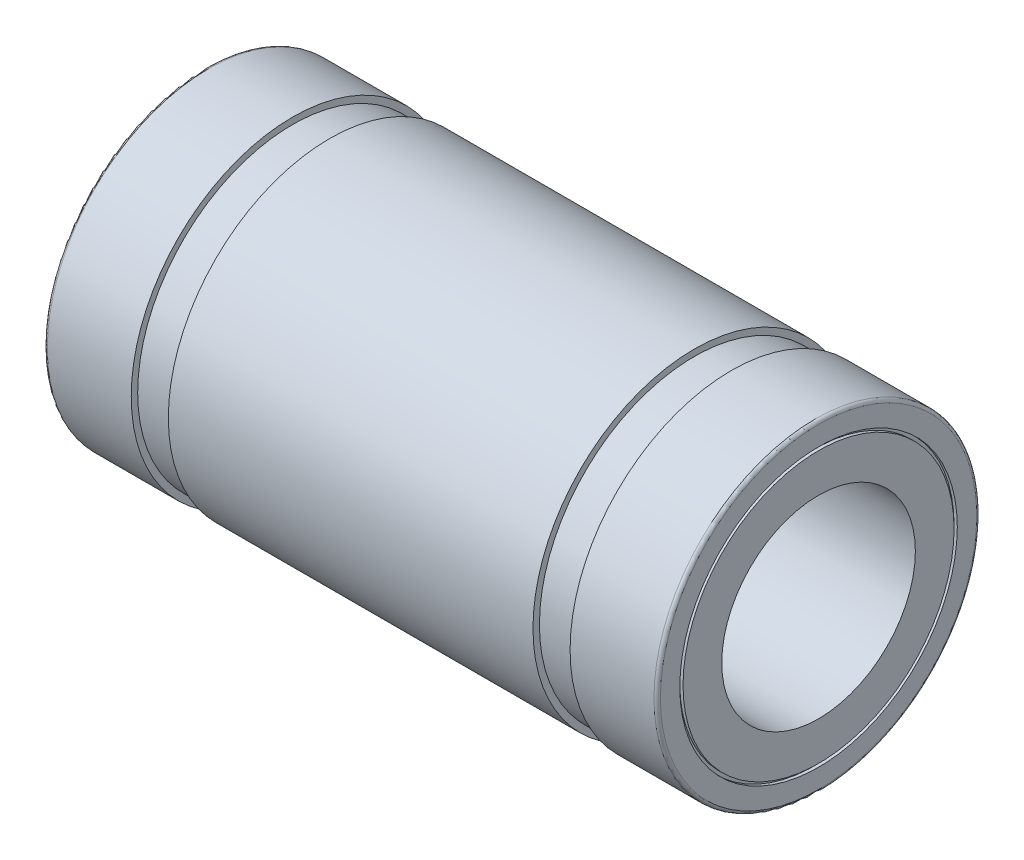
SolidWorks part; units mm, degrees
ref_plane "Front Plane" through (0, 0, 0) normal (0, 0, 1) x (1, 0, 0)
ref_plane "Top Plane" through (0, 0, 0) normal (0, 1, 0) x (1, 0, 0)
ref_plane "Right Plane" through (0, 0, 0) normal (1, 0, 0) x (0, 0, -1)
ref_plane "Plane1" through (0, 0, 0) normal (0, 0, -1) x (-1, 0, 0)
sketch "Sketch1" plane through (0, 0, 0) normal (0, 0, -1) x (-1, 0, 0)
  line L0 (-9.4, 4.2) -> (-9.5, 4.2)
  line L1 (-9.5, 4.2) -> (-9.5, 3)
  line L2 (-9.5, 3) -> (9.5, 3)
  line L3 (9.5, 3) -> (9.5, 4.2)
  line L4 (9.5, 4.2) -> (9.4, 4.2)
  line L5 (9.4, 4.2) -> (9.4, 4.3)
  line L6 (9.4, 4.3) -> (9.5, 4.3)
  line L7 (9.5, 4.3) -> (9.5, 4.9)
  line L8 (9.4, 5) -> (6.8, 5)
  line L9 (6.8, 5) -> (6.8, 4.8)
  line L10 (6.8, 4.8) -> (5.65, 4.8)
  line L11 (5.65, 4.8) -> (5.65, 5)
  line L12 (5.65, 5) -> (-5.65, 5)
  line L13 (-5.65, 5) -> (-5.65, 4.8)
  line L14 (-5.65, 4.8) -> (-6.8, 4.8)
  line L15 (-6.8, 4.8) -> (-6.8, 5)
  line L16 (-6.8, 5) -> (-9.4, 5)
  line L17 (-9.5, 4.9) -> (-9.5, 4.3)
  line L18 (-9.5, 4.3) -> (-9.4, 4.3)
  line L19 (-9.4, 4.3) -> (-9.4, 4.2)
  line L20 (-9.5, 0) -> (9.5, 0) construction
  arc A0 (9.5, 4.9) -> (9.4, 5) centre (9.4, 4.9) ccw
  arc A1 (-9.4, 5) -> (-9.5, 4.9) centre (-9.4, 4.9) ccw
revolve "Revolve1" add sketch "Sketch1" angle 360 about L20
